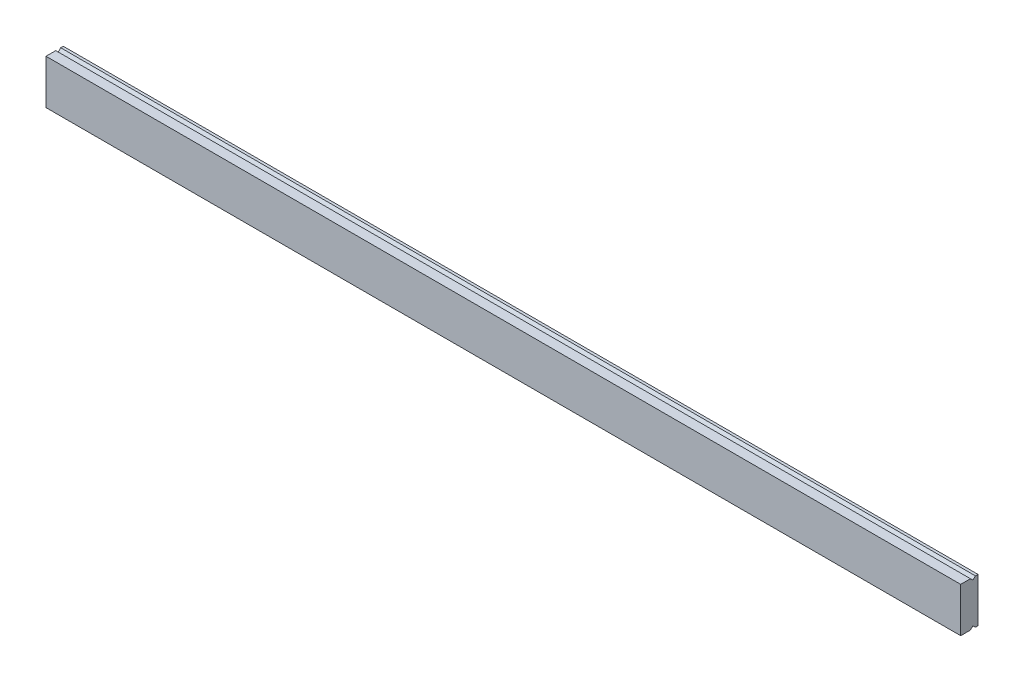
SolidWorks part; units mm, degrees
ref_plane "前视基准面" through (0, 0, 0) normal (0, 0, 1) x (1, 0, 0)
ref_plane "上视基准面" through (0, 0, 0) normal (0, 1, 0) x (1, 0, 0)
ref_plane "右视基准面" through (0, 0, 0) normal (1, 0, 0) x (0, 0, -1)
ref_plane "基准面4" through (95, 0, 0) normal (-1, 0, 0) x (0, -1, 0)
sketch "草图1" plane through (95, 0, 0) normal (-1, 0, 0) x (0, -1, 0)
  line L0 (-249, 463) -> (-231, 463)
  line L1 (-231, 463) -> (-231, 464.05)
  line L2 (-231, 464.05) -> (-232, 465.05)
  line L3 (-232, 465.05) -> (-231, 466.05)
  line L4 (-231, 466.05) -> (-231, 470)
  line L5 (-231, 470) -> (-249, 470)
  line L6 (-249, 470) -> (-249, 466.05)
  line L7 (-249, 466.05) -> (-248, 465.05)
  line L8 (-248, 465.05) -> (-249, 464.05)
  line L9 (-249, 464.05) -> (-249, 463)
extrude "凸台-拉伸1" add sketch "草图1" against normal blind 370
